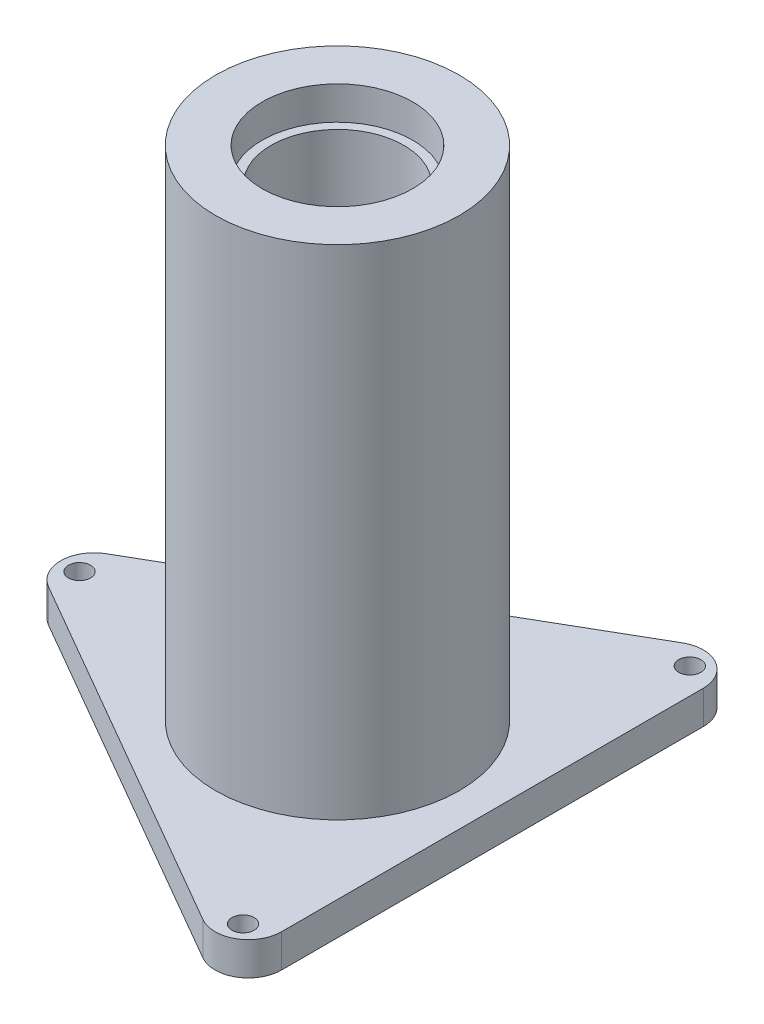
SolidWorks part; units mm, degrees
ref_plane "Front Plane" through (0, 0, 0) normal (0, 0, 1) x (1, 0, 0)
ref_plane "Top Plane" through (0, 0, 0) normal (0, 1, 0) x (1, 0, 0)
ref_plane "Right Plane" through (0, 0, 0) normal (1, 0, 0) x (0, 0, -1)
sketch "Sketch1" plane through (0, 0, 0) normal (0, 0, 1) x (1, 0, 0)
  line L0 (0, 17.7187) -> (0, -16.5312) construction
  line L1 (11, 12.2812) -> (6.8, 12.2812)
  line L2 (6.8, 12.2812) -> (6.8, 9.2812)
  line L3 (6.8, 9.2812) -> (6, 9.2812)
  line L4 (6, 9.2812) -> (6, -32.7188)
  line L7 (6, -32.7188) -> (11, -32.7188)
  line L8 (11, -32.7188) -> (11, 12.2812)
  dimension "D1" = 12
  dimension "D2" = 0.8
  dimension "D3" = 5
  dimension "D4" = 45
  dimension "D5" = 3
revolve "Revolve1" add sketch "Sketch1" angle 360 about L0
sketch "Sketch2" plane through (0, -32.7188, 0) normal (0, -1, 0) x (1, 0, 0)
  line L0 (-23.3, 0) -> (0, 0) construction
  line L4 (-23.3, 0) -> (11.65, -20.1784) construction
  line L5 (11.65, -20.1784) -> (11.65, 20.1784) construction
  line L6 (11.65, 20.1784) -> (-23.3, 0) construction
  line L7 (-23.5, -2.5981) -> (9.5, -21.6506)
  line L8 (14, -19.0526) -> (14, 19.0526)
  line L9 (9.5, 21.6506) -> (-23.5, 2.5981)
  circle A0 centre (0, 0) radius 14 construction
  circle A5 centre (0, 0) radius 6.8
  circle A6 centre (0, 0) radius 11.65 construction
  circle A7 centre (11.65, 20.1784) radius 1
  circle A8 centre (-23.3, 0) radius 1
  circle A9 centre (11.65, -20.1784) radius 1
  arc A10 (9.5, -21.6506) -> (14, -19.0526) centre (11, -19.0526) ccw
  arc A11 (-23.5, -2.5981) -> (-23.5, 2.5981) centre (-22, 0) cw
  arc A12 (14, 19.0526) -> (9.5, 21.6506) centre (11, 19.0526) ccw
  dimension "D1" = 28
  dimension "D2" = 2
  dimension "D3" = 2
  dimension "D4" = 2
  dimension "D6" = 3
  dimension "D5" = 23.3
extrude "Boss-Extrude1" add sketch "Sketch2" along normal blind 3
